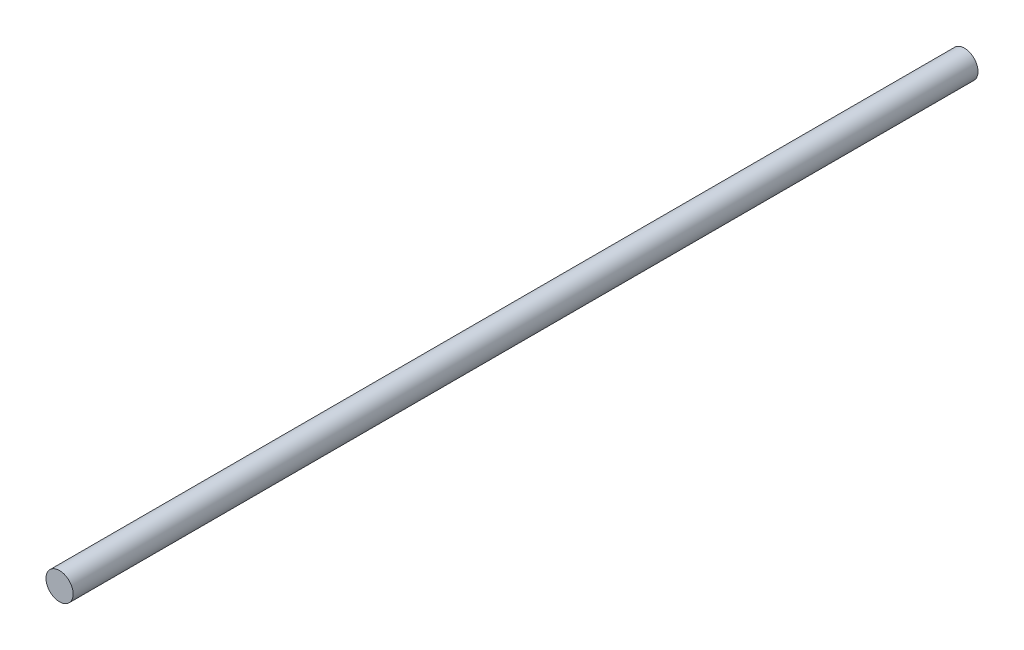
SolidWorks part; units mm, degrees
ref_plane "Front Plane" through (0, 0, 0) normal (0, 0, 1) x (1, 0, 0)
ref_plane "Top Plane" through (0, 0, 0) normal (0, 1, 0) x (1, 0, 0)
ref_plane "Right Plane" through (0, 0, 0) normal (1, 0, 0) x (0, 0, -1)
sketch "Sketch1" plane through (0, 0, 0) normal (0, 0, 1) x (1, 0, 0)
  circle A0 centre (0, 0) radius 6
extrude "Boss-Extrude1" add sketch "Sketch1" along normal blind 400
